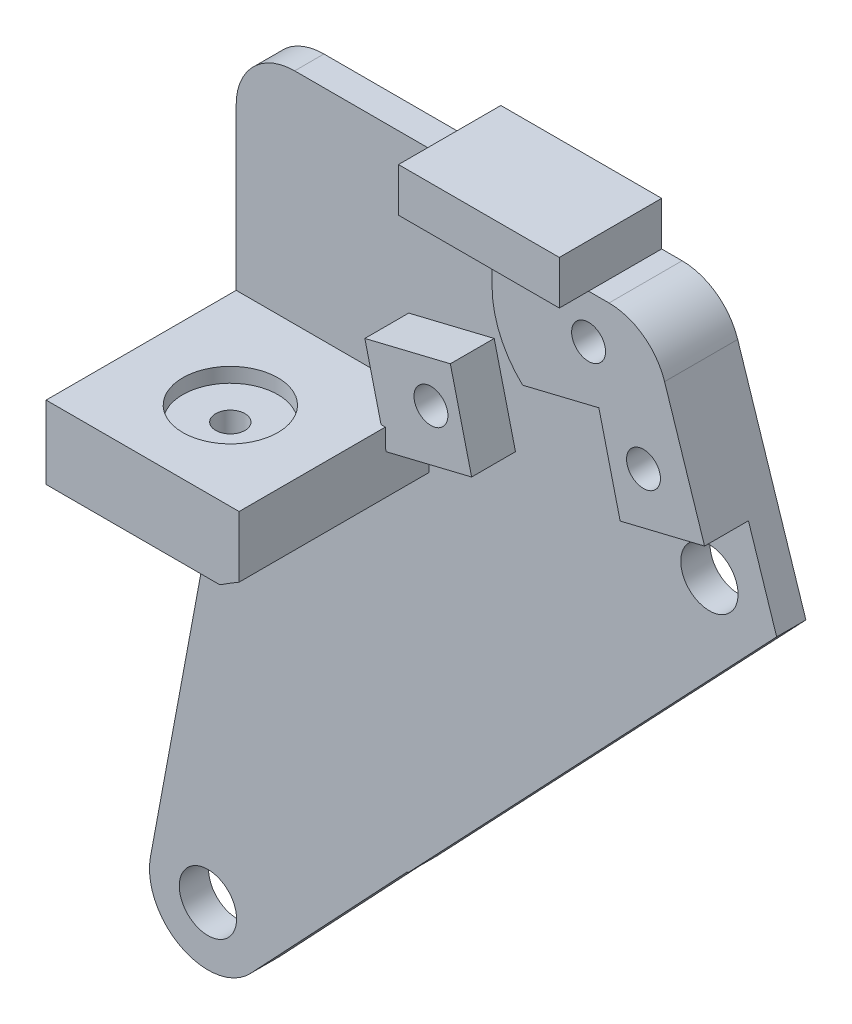
SolidWorks part; units mm, degrees
ref_plane "Front Plane" through (0, 0, 0) normal (0, 0, 1) x (1, 0, 0)
ref_plane "Top Plane" through (0, 0, 0) normal (0, 1, 0) x (1, 0, 0)
ref_plane "Right Plane" through (0, 0, 0) normal (1, 0, 0) x (0, 0, -1)
sketch "Sketch1" plane through (0, 0, 0) normal (0, 0, 1) x (1, 0, 0)
  line L12 (-28.2, 23.755) -> (-28.2, -23.755)
  line L13 (-23.755, -28.2) -> (23.755, -28.2)
  line L14 (28.2, -23.755) -> (28.2, 23.755)
  line L15 (23.755, 28.2) -> (-23.755, 28.2)
  circle A0 centre (0, 0) radius 19.05
  circle A1 centre (-23.57, 23.57) radius 2.55
  circle A2 centre (23.57, 23.57) radius 2.55
  circle A3 centre (23.57, -23.57) radius 2.55
  circle A4 centre (-23.57, -23.57) radius 2.55
  arc A12 (-23.755, 28.2) -> (-28.2, 23.755) centre (-23.755, 23.755) ccw
  arc A13 (-28.2, -23.755) -> (-23.755, -28.2) centre (-23.755, -23.755) ccw
  arc A14 (23.755, -28.2) -> (28.2, -23.755) centre (23.755, -23.755) ccw
  arc A15 (28.2, 23.755) -> (23.755, 28.2) centre (23.755, 23.755) ccw
sketch "Sketch2" plane through (0, 0, 0) normal (0, 0, 1) x (1, 0, 0)
  line L0 (-33.02, 0) -> (-33.02, 66.04) construction
  line L1 (-17.0688, -8.4592) -> (-41.402, 40.64)
  line L2 (-41.402, 66.04) -> (-1.524, 66.04)
  line L3 (-1.524, 66.04) -> (18.1091, 5.9131)
  line L4 (-41.402, 40.64) -> (-41.402, 66.04)
  arc A0 (-17.0688, -8.4592) -> (18.1091, 5.9131) centre (0, 0) ccw
  circle A1 centre (0, 0) radius 33.02 construction
  circle A2 centre (0, 0) radius 38.1 construction
  circle A3 centre (0, 0) radius 3.81
  dimension "D1" = 38.1
  dimension "D2" = 66.04
  dimension "D3" = 66.04
  dimension "D5" = 76.2
  dimension "D8" = 7.62
  dimension "D4" = 39.878
  dimension "D6" = 8.382
  dimension "D7" = 25.4
extrude "Boss-Extrude1" add sketch "Sketch2" along normal blind 2.54
sketch "Sketch5" plane through (0, 0, 2.54) normal (0, 0, 1) x (1, 0, 0)
  line L0 (-33.02, 0) -> (-33.02, 66.04) construction
  line L1 (-24.638, 40.64) -> (-41.402, 40.64)
  line L2 (-24.638, 40.64) -> (-24.638, 46.99)
  line L3 (-24.638, 46.99) -> (-41.402, 46.99)
  line L4 (-41.402, 40.64) -> (-41.402, 46.99)
  line L5 (-24.638, 40.64) -> (-41.402, 46.99) construction
  line L6 (-24.638, 46.99) -> (-41.402, 40.64) construction
  point P0 (-33.02, 43.815)
  dimension "D1" = 6.35
extrude "Boss-Extrude2" add sketch "Sketch5" along normal blind 16.51
sketch "Sketch6" plane through (0, 46.99, 0) normal (0, 1, 0) x (1, 0, 0)
  line L0 (-33.02, -2.54) -> (-33.02, -19.05) construction
  line L1 (-24.638, -2.54) -> (-41.402, -2.54) construction
  line L2 (-24.638, -19.05) -> (-41.402, -19.05) construction
  line L3 (-1.524, -2.54) -> (-41.402, -2.54) construction
  circle A0 centre (-33.02, -11.43) radius 4.1275
  dimension "D1" = 8.255
  dimension "0.4" = 8.89
extrude "Cut-Extrude2" cut sketch "Sketch6" against normal blind 1.27
sketch "Sketch7" plane through (0, 45.72, 0) normal (0, 1, 0) x (1, 0, 0)
  circle A0 centre (-33.02, -11.43) radius 1.27
  dimension "D1" = 2.54
extrude "Cut-Extrude3" cut sketch "Sketch7" against normal through all
sketch "Sketch9" plane through (0, 0, 0) normal (0, 0, -1) x (-1, 0, 0)
  line L0 (6.9839, 62.23) -> (3.1711, 62.23) construction
  line L1 (3.1711, 62.23) -> (5.0775, 58.928)
  line L2 (5.0775, 58.928) -> (8.8904, 58.928)
  line L3 (8.8904, 58.928) -> (10.7968, 62.23)
  line L4 (10.7968, 62.23) -> (8.8904, 65.532)
  line L5 (8.8904, 65.532) -> (5.0775, 65.532)
  line L6 (5.0775, 65.532) -> (3.1711, 62.23)
  line L7 (6.9839, 60.5028) -> (6.9839, 63.9572) construction
  line L8 (24.3799, 49.664) -> (23.3081, 53.3231)
  line L9 (23.3081, 53.3231) -> (19.6034, 54.2245)
  line L10 (19.6034, 54.2245) -> (16.9704, 51.4668)
  line L11 (16.9704, 51.4668) -> (18.0421, 47.8077)
  line L12 (18.0421, 47.8077) -> (21.7469, 46.9063)
  line L13 (21.7469, 46.9063) -> (24.3799, 49.664)
  line L14 (5.9185, 54.1558) -> (4.8467, 57.8149)
  line L15 (4.8467, 57.8149) -> (1.142, 58.7163)
  line L16 (1.142, 58.7163) -> (-1.491, 55.9586)
  line L17 (-1.491, 55.9586) -> (-0.4193, 52.2995)
  line L18 (-0.4193, 52.2995) -> (3.2855, 51.3981)
  line L19 (3.2855, 51.3981) -> (5.9185, 54.1558)
  line L21 (24.9034, 50.8527) -> (-13.9627, 60.3092) construction
  circle A0 centre (6.9839, 62.23) radius 3.302 construction
  circle A1 centre (20.6751, 50.5654) radius 3.302 construction
  circle A2 centre (2.2137, 55.0572) radius 3.302 construction
  circle A3 centre (6.9839, 62.23) radius 1.7272 construction
  circle A4 centre (2.2137, 55.0572) radius 1.5 construction
  circle A5 centre (20.6751, 50.5654) radius 1.5 construction
  dimension "D1" = 6.604
  dimension "D2" = 6.604
  dimension "D3" = 6.604
extrude "Cut-Extrude4" cut sketch "Sketch9" against normal blind 2.286
sketch "Sketch8" plane through (0, 0, 2.54) normal (0, 0, 1) x (1, 0, 0)
  line L0 (-41.402, 66.04) -> (-1.524, 66.04) construction
  line L1 (-15.367, 66.04) -> (-6.9839, 66.04)
  line L2 (-15.367, 66.04) -> (-15.367, 62.23)
  line L3 (-14.4512, 58.42) -> (-6.9839, 58.42) construction
  line L4 (-6.9839, 66.04) -> (-6.9839, 58.42) construction
  line L5 (-15.875, 63.5) -> (-15.875, 55.88) construction
  line L6 (-18.9903, 54.5774) -> (0.6579, 59.358) construction
  line L8 (-15.367, 62.23) -> (-6.9839, 62.23) construction
  line L9 (-6.9839, 66.04) -> (-1.524, 66.04)
  line L10 (-1.524, 66.04) -> (3.0918, 51.9041)
  line L11 (18.1091, 5.9131) -> (-1.524, 66.04) construction
  line L12 (-5.8104, 55.4982) -> (-4.2737, 49.1825) construction
  line L13 (-1.524, 66.04) -> (18.1091, 5.9131) construction
  line L14 (-4.2737, 49.1825) -> (-16.6817, 46.1635) construction
  line L15 (-16.6817, 46.1635) -> (-18.7435, 54.6374) construction
  line L16 (-6.0887, 57.7165) -> (-4.2404, 50.1201)
  line L17 (-17.142, 46.981) -> (-18.9903, 54.5774)
  line L18 (3.0918, 51.9041) -> (-4.2404, 50.1201)
  line L19 (-24.9034, 53.1387) -> (13.9627, 62.5952) construction
  line L20 (-5.5636, 55.5583) -> (-4.0269, 49.2425) construction
  line L21 (-12.7085, 56.1058) -> (-6.0887, 57.7165)
  line L22 (-16.9285, 46.1034) -> (-18.9903, 54.5774) construction
  line L23 (-17.142, 46.981) -> (-24.5674, 45.1744)
  line L24 (-24.5674, 45.1744) -> (-26.4157, 52.7707)
  line L25 (-26.4157, 52.7707) -> (-18.9903, 54.5774)
  line L26 (-21.1208, 35.3063) -> (-24.9034, 50.8527) construction
  line L27 (0.4193, 52.2995) -> (-3.2855, 51.3981) construction
  arc A0 (-6.9839, 58.42) -> (-6.9839, 66.04) centre (-6.9839, 62.23) ccw construction
  circle A1 centre (-20.6751, 50.5654) radius 3.4925 construction
  circle A2 centre (-2.2137, 55.0572) radius 3.4925 construction
  arc A3 (-15.367, 62.23) -> (-12.7085, 56.1058) centre (-6.9839, 62.23) ccw
  point P29 (-6.9839, 62.23)
  point P50 (-20.6751, 50.5654)
  point P52 (-2.2137, 55.0572)
  dimension "D2" = 6.985
  dimension "D3" = 6.985
  dimension "D1" = 0.508
  dimension "D4" = 0.254
  dimension "D5" = 1.016
  dimension "D6" = 1.016
extrude "Boss-Extrude3" add sketch "Sketch8" along normal blind 3.81
hole_wizard "#4 Clearance Hole1" positions "Sketch11" profile "Sketch10" hole size "#4" standard "ANSI Inch" end condition through all
sketch "Sketch11" plane through (0, 0, 6.35) normal (0, 0, 1) x (1, 0, 0)
  point P0 (-6.9839, 62.23)
  point P4 (-20.6751, 50.5654)
  point P7 (-2.2137, 55.0572)
sketch "Sketch10" plane through (-6.9839, 62.23, 6.35) normal (1, 0, 0) x (0, -1, 0)
  line L0 (0, 0) -> (0, 6.35)
  line L1 (0, 6.35) -> (1.4732, 6.35)
  line L2 (1.4732, 6.35) -> (1.4732, 0)
  line L5 (1.4732, 0) -> (0, 0)
  line L11 (0, -6.35) -> (0, 107.95) construction
  dimension "Thru Hole Dia." = 2.9464
  dimension "Thru Hole Depth" = 6.35
sketch "Sketch14" plane through (0, 0, 2.54) normal (0, 0, 1) x (1, 0, 0)
  line L1 (-41.402, 66.04) -> (-1.524, 66.04) construction
  line L2 (-6.9839, 60.7568) -> (-6.9839, 66.04) construction
  line L3 (-6.9839, 66.04) -> (-20.9539, 66.04)
  line L6 (-6.9839, 66.04) -> (-6.9839, 69.85)
  line L8 (-6.9839, 69.85) -> (-20.9539, 69.85)
  line L9 (-20.9539, 66.04) -> (-20.9539, 69.85)
  circle A0 centre (-6.9839, 62.23) radius 1.4732 construction
  point P0 (-6.9839, 62.23)
  dimension "D1" = 3.81
  dimension "D2" = 13.97
extrude "Boss-Extrude6" add sketch "Sketch14" along normal blind 6.35 and the other way through all
fillet "Fillet1" radius 5.08 4 edges at (-41.402, 66.04, 1.27) (-1.524, 66.04, 3.175)
sketch "Sketch15" plane through (0, 0, 2.54) normal (0, 0, 1) x (1, 0, 0)
  line L0 (-17.0688, -8.4592) -> (-41.402, 40.64) construction
  line L1 (-1.524, 66.04) -> (18.1091, 5.9131) construction
  arc A0 (-31.9429, 32.9938) -> (-0.299, 45.9222) centre (0, 0) cw construction
  circle A1 centre (0, 0) radius 3.81 construction
  arc A2 (-0.3152, 48.4114) -> (-33.6744, 34.7821) centre (0, 0) ccw
  arc A3 (-0.2828, 43.4331) -> (-30.2115, 31.2054) centre (0, 0) ccw
  arc A4 (-0.2828, 43.4331) -> (-0.3152, 48.4114) centre (-0.299, 45.9222) ccw
  arc A5 (-33.6744, 34.7821) -> (-30.2115, 31.2054) centre (-31.9429, 32.9938) ccw
  point P6 (-17.3687, 42.512)
  dimension "D1" = 4.9784
  dimension "D4" = 45.9232
  dimension "D2" = 5.08
  dimension "D3" = 5.08
extrude "Cut-Extrude5" cut sketch "Sketch15" against normal through all both and the other way through all
sketch "Sketch19" plane through (0, 0, 2.54) normal (0, 0, 1) x (1, 0, 0)
  line L0 (-0.299, 45.9222) -> (0, 0) construction
  line L1 (0, 0) -> (-48.9345, -0.3186) construction
  line L2 (-0.299, 45.9222) -> (-43.8546, -0.2855) construction
  line L3 (5.4662, 44.6323) -> (-40.158, -3.77)
  line L4 (3.3977, 42.4378) -> (-40.158, -3.77) construction
  line L5 (-1.524, 66.04) -> (18.1091, 5.9131) construction
  line L6 (-48.8488, 0.6444) -> (-41.402, 40.64)
  line L7 (-17.0688, -8.4592) -> (-41.402, 40.64) construction
  line L8 (-41.402, 40.64) -> (-26.3088, 40.64) construction
  line L9 (5.4662, 44.6323) -> (3.0918, 51.9041)
  line L10 (-4.2404, 50.1201) -> (3.0918, 51.9041) construction
  line L11 (3.0918, 51.9041) -> (-41.402, 40.64)
  circle A0 centre (-0.299, 45.9222) radius 2.4892
  circle A1 centre (-43.8546, -0.2855) radius 2.4892
  arc A2 (-48.8488, 0.6444) -> (-40.158, -3.77) centre (-43.8546, -0.2855) ccw
  dimension "D4" = 4.9784
  dimension "D5" = 5.08
  dimension "D1" = 90
  dimension "D2" = 45.9222
  dimension "D3" = 63.5
extrude "Boss-Extrude8" add sketch "Sketch19" against normal through all contours L6 L11 L9 L3 A2
sketch "Sketch20" plane through (0, 0, 2.54) normal (0, 0, 1) x (1, 0, 0)
  line L0 (-40.158, -3.77) -> (10.7295, 49.8638)
  line L1 (-40.158, -3.77) -> (-26.5483, 10.6684) construction
  line L2 (10.7295, 49.8638) -> (48.0717, 14.4336)
  line L3 (48.0717, 14.4336) -> (-7.6731, -44.3196)
  line L4 (-7.6731, -44.3196) -> (-40.158, -3.77)
  arc A0 (-48.8488, 0.6444) -> (-40.158, -3.77) centre (-43.8546, -0.2855) ccw construction
extrude "Cut-Extrude8" cut sketch "Sketch20" against normal blind 2.54
sketch "Sketch18" plane through (0, 0, 2.54) normal (0, 0, 1) x (1, 0, 0)
  line L0 (-1.524, 66.04) -> (18.1091, 5.9131) construction
  line L1 (-17.0688, -8.4592) -> (-41.402, 40.64) construction
  line L2 (3.7043, 50.028) -> (2.6806, 53.1633)
  line L3 (-37.676, 33.1217) -> (-39.1405, 36.0768)
  arc A0 (-31.9429, 32.9938) -> (-0.299, 45.9222) centre (0, 0) cw
  arc A1 (-0.299, 45.9222) -> (-31.9429, 32.9938) centre (0, 0) ccw construction
  arc A2 (-37.676, 33.1217) -> (3.7043, 50.028) centre (0, 0) cw
  arc A3 (-29.0124, 35.598) -> (-5.9439, 45.5369) centre (0, 0) cw construction
  arc A4 (-31.6922, 38.8861) -> (-6.4929, 49.743) centre (0, 0) cw construction
  arc A5 (-39.1405, 36.0768) -> (2.6806, 53.1633) centre (0, 0) cw
  arc A6 (-39.9785, 35.1459) -> (3.9307, 53.0855) centre (0, 0) cw construction
  point P20 (-25.0092, 46.99)
  line M10 (-24.638, 45.4645) -> (-24.638, 41.6741)
  line M11 (-26.3088, 40.64) -> (-41.402, 40.64)
  line M12 (-26.5483, 10.6684) -> (-26.5176, 10.6065)
  line M14 (5.5429, 44.3973) -> (3.0918, 51.9041)
  line M15 (3.0918, 51.9041) -> (-4.2404, 50.1201)
  line M16 (-4.2404, 50.1201) -> (-6.0887, 57.7165)
  line M22 (-17.142, 46.981) -> (-24.5674, 45.1744)
  line M23 (-24.5674, 45.1744) -> (-24.638, 45.4645)
  line M25 (-18.9903, 54.5774) -> (-17.142, 46.981)
  dimension "D1" = 4.2418
extrude "Boss-Extrude7" [suppressed] add sketch "Sketch18" along normal blind 3.81 contours A5 A2 M12 M11 | A5 A2 M10 M14 M15 M16 M25 M22 M23 | A2 M10 M22 M23
sketch "Sketch16" plane through (0, 0, 2.54) normal (0, 0, 1) x (1, 0, 0)
  arc A0 (-31.9429, 32.9938) -> (-0.299, 45.9222) centre (0, 0) cw construction
  arc A1 (-0.3266, 50.1639) -> (-34.8934, 36.0413) centre (0, 0) ccw
  arc A2 (-0.2713, 41.6805) -> (-28.9925, 29.9462) centre (0, 0) ccw
  arc A3 (-0.2713, 41.6805) -> (-0.3266, 50.1639) centre (-0.299, 45.9222) ccw
  arc A4 (-34.8934, 36.0413) -> (-28.9925, 29.9462) centre (-31.9429, 32.9938) ccw
  point P3 (-17.3687, 42.512)
  dimension "D3" = 45.9232
  dimension "D1" = 8.4836
  dimension "D2" = 43.7
extrude "Cut-Extrude7" [suppressed] cut sketch "Sketch16" along normal through all
sketch "Sketch13" plane through (0, 0, 0) normal (0, 0, -1) x (-1, 0, 0)
  line L0 (-5.5429, 44.3973) -> (26.5176, 10.6065) construction
  line L1 (41.402, 66.04) -> (1.524, 66.04) construction
  circle A0 centre (14.2843, 23.5001) radius 6.35
  circle A1 centre (21.463, 66.04) radius 6.35
  circle A2 centre (41.402, 40.64) radius 6.35
  dimension "D1" = 12.7
  dimension "D2" = 12.7
  dimension "D3" = 12.7
extrude "Print Tabs" [suppressed] add sketch "Sketch13" against normal blind 0.4
mirror "Mirror1" [suppressed] about plane through (0, 0, 0) normal (1, 0, 0)
